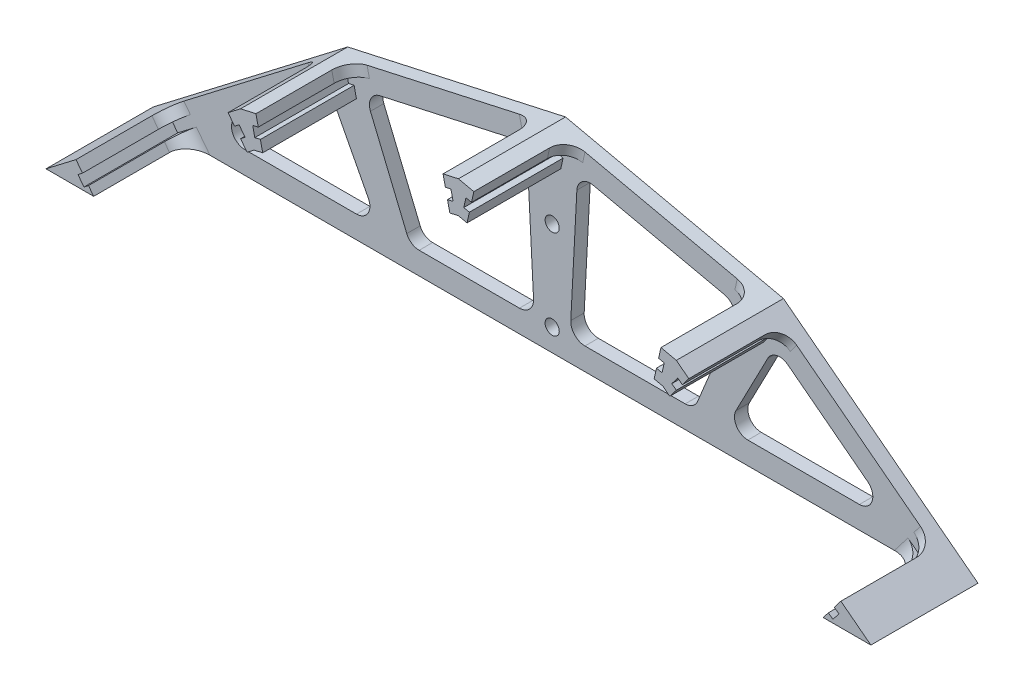
SolidWorks part; units mm, degrees
ref_plane "Front Plane" through (0, 0, 0) normal (0, 0, 1) x (1, 0, 0)
ref_plane "Top Plane" through (0, 0, 0) normal (0, 1, 0) x (1, 0, 0)
ref_plane "Right Plane" through (0, 0, 0) normal (1, 0, 0) x (0, 0, -1)
sketch "Sketch1" plane through (0, 0, 0) normal (0, 0, 1) x (1, 0, 0)
  line L0 (0, -57.7528) -> (0, 57.7528) construction
  line L2 (88.4825, 16.4928) -> (0, -57.7528) construction
  line L3 (0, 57.7528) -> (48.8148, 46.9308)
  line L4 (48.8148, 46.9308) -> (0, -57.7528) construction
  line L5 (48.8148, 46.9308) -> (88.4825, 16.4928)
  line L7 (-48.8148, 46.9308) -> (-88.4825, 16.4928)
  line L8 (-48.8148, 46.9308) -> (0, -57.7528) construction
  line L9 (0, 57.7528) -> (-48.8148, 46.9308)
  line L10 (-88.4825, 16.4928) -> (0, -57.7528) construction
  line L11 (-84.4891, 13.484) -> (84.4891, 13.484)
  line L12 (-84.4891, 13.484) -> (-92.4036, 13.484)
  line L13 (-92.4036, 13.484) -> (-88.4825, 16.4928)
  line L14 (84.4891, 13.484) -> (92.4036, 13.484)
  line L15 (92.4036, 13.484) -> (88.4825, 16.4928)
  dimension "D2" = 25
  dimension "D3" = 25
  dimension "D4" = 50
  dimension "D1" = 5
extrude "Boss-Extrude1" add sketch "Sketch1" along normal blind 3
sketch "Sketch2" plane through (0, 0, 3) normal (0, 0, 1) x (1, 0, 0)
  line L0 (-48.8148, 46.9308) -> (-45.3685, 47.6949)
  line L1 (0, 57.7528) -> (-48.8148, 46.9308) construction
  line L2 (-45.3685, 47.6949) -> (-44.849, 45.3518)
  line L3 (-43.8534, 40.8608) -> (-47.2997, 40.0968)
  line L4 (-47.2997, 40.0968) -> (-48.8148, 46.9308) construction
  line L5 (-3.8427, 53.316) -> (-1.4391, 53.8488) construction
  line L6 (1.5151, 50.9188) -> (0, 57.7528) construction
  line L7 (-1.9312, 50.1547) -> (1.5151, 50.9188)
  line L8 (-2.4507, 52.4978) -> (-1.9312, 50.1547)
  line L9 (-24.4074, 52.3418) -> (-20.3059, 33.8411) construction
  line L10 (0, 57.7528) -> (-48.8148, 46.9308) construction
  line L11 (-46.0987, 45.0747) -> (-45.6225, 42.9269)
  line L12 (-44.849, 45.3518) -> (-46.0987, 45.0747)
  line L13 (-43.4571, 44.5337) -> (-45.8606, 44.0008) construction
  line L14 (-44.3729, 43.2039) -> (-45.6225, 42.9269)
  line L15 (-44.3729, 43.2039) -> (-43.8534, 40.8608)
  line L16 (-2.4507, 52.4978) -> (-1.201, 52.7749)
  line L17 (-2.9269, 54.6457) -> (-1.6772, 54.9227)
  line L18 (-1.6772, 54.9227) -> (-1.201, 52.7749)
  line L19 (-3.4463, 56.9888) -> (-2.9269, 54.6457)
  line L20 (0, 57.7528) -> (-3.4463, 56.9888)
  line L21 (0, 57.7528) -> (0, -57.7528) construction
  line L22 (43.4571, 44.5337) -> (45.8606, 44.0008) construction
  line L23 (24.4074, 52.3418) -> (20.3059, 33.8411) construction
  line L24 (1.9312, 50.1547) -> (-1.5151, 50.9188)
  line L25 (-1.5151, 50.9188) -> (0, 57.7528) construction
  line L26 (3.8427, 53.316) -> (1.4391, 53.8488) construction
  line L27 (47.2997, 40.0968) -> (48.8148, 46.9308) construction
  line L28 (43.8534, 40.8608) -> (47.2997, 40.0968)
  line L29 (0, 57.7528) -> (3.4463, 56.9888)
  line L30 (3.4463, 56.9888) -> (2.9269, 54.6457)
  line L31 (1.6772, 54.9227) -> (1.201, 52.7749)
  line L32 (2.9269, 54.6457) -> (1.6772, 54.9227)
  line L33 (2.4507, 52.4978) -> (1.201, 52.7749)
  line L34 (44.3729, 43.2039) -> (43.8534, 40.8608)
  line L35 (44.3729, 43.2039) -> (45.6225, 42.9269)
  line L36 (44.849, 45.3518) -> (46.0987, 45.0747)
  line L37 (46.0987, 45.0747) -> (45.6225, 42.9269)
  line L38 (2.4507, 52.4978) -> (1.9312, 50.1547)
  line L39 (45.3685, 47.6949) -> (44.849, 45.3518)
  line L40 (48.8148, 46.9308) -> (45.3685, 47.6949)
  line L41 (48.8148, 46.9308) -> (0, -57.7528) construction
  line L42 (0, -57.7528) -> (-48.8148, 46.9308) construction
  line L43 (-82.2734, 13.2605) -> (-88.4825, 16.4928) construction
  line L44 (-50.4223, 41.2857) -> (-48.4692, 42.7844) construction
  line L45 (-68.6486, 31.7118) -> (-57.1127, 16.6778) construction
  line L46 (-81.4206, 13.0882) -> (-84.2211, 10.9393)
  line L47 (-84.2211, 10.9393) -> (-88.4825, 16.4928)
  line L48 (-82.6136, 16.5845) -> (-84.5668, 15.0858) construction
  line L49 (-44.5535, 41.3774) -> (-48.8148, 46.9308) construction
  line L50 (-47.354, 39.2284) -> (-44.5535, 41.3774)
  line L51 (-88.4825, 16.4928) -> (-85.6819, 18.6417)
  line L52 (-85.6819, 18.6417) -> (-84.2209, 16.7377)
  line L53 (-85.2364, 15.9584) -> (-83.8971, 14.2131)
  line L54 (-84.2209, 16.7377) -> (-85.2364, 15.9584)
  line L55 (-82.8816, 14.9923) -> (-83.8971, 14.2131)
  line L56 (-48.815, 41.1325) -> (-47.354, 39.2284)
  line L57 (-48.815, 41.1325) -> (-47.7995, 41.9117)
  line L58 (-50.1543, 42.8779) -> (-49.1388, 43.6571)
  line L59 (-49.1388, 43.6571) -> (-47.7995, 41.9117)
  line L60 (-82.8816, 14.9923) -> (-81.4206, 13.0882)
  line L61 (-51.6153, 44.7819) -> (-50.1543, 42.8779)
  line L62 (-48.8148, 46.9308) -> (-51.6153, 44.7819)
  line L63 (47.354, 39.2284) -> (44.5535, 41.3774)
  line L64 (44.5535, 41.3774) -> (48.8148, 46.9308) construction
  line L65 (82.6136, 16.5845) -> (84.5668, 15.0858) construction
  line L66 (84.2211, 10.9393) -> (88.4825, 16.4928)
  line L67 (81.4206, 13.0882) -> (84.2211, 10.9393)
  line L68 (68.6486, 31.7118) -> (57.1127, 16.6778) construction
  line L69 (50.4223, 41.2857) -> (48.4692, 42.7844) construction
  line L70 (48.8148, 46.9308) -> (51.6153, 44.7819)
  line L71 (51.6153, 44.7819) -> (50.1543, 42.8779)
  line L72 (82.8816, 14.9923) -> (81.4206, 13.0882)
  line L73 (49.1388, 43.6571) -> (47.7995, 41.9117)
  line L74 (50.1543, 42.8779) -> (49.1388, 43.6571)
  line L75 (48.815, 41.1325) -> (47.7995, 41.9117)
  line L76 (48.815, 41.1325) -> (47.354, 39.2284)
  line L77 (82.8816, 14.9923) -> (83.8971, 14.2131)
  line L78 (84.2209, 16.7377) -> (85.2364, 15.9584)
  line L79 (85.2364, 15.9584) -> (83.8971, 14.2131)
  line L80 (85.6819, 18.6417) -> (84.2209, 16.7377)
  line L81 (88.4825, 16.4928) -> (85.6819, 18.6417)
  line L82 (-43.4571, 44.5337) -> (-50.1313, 43.054) construction
  line L83 (-88.4825, 16.4928) -> (-92.4036, 13.484)
  line L84 (-92.4036, 13.484) -> (-86.1738, 13.484)
  line L85 (-92.4036, 13.484) -> (92.4036, 13.484) construction
  line L86 (-86.1738, 13.484) -> (-88.4825, 16.4928)
  line L87 (84.2211, 10.9393) -> (88.4825, 16.4928)
  line L88 (92.4036, 13.484) -> (86.1738, 13.484)
  line L89 (88.4825, 16.4928) -> (92.4036, 13.484)
  point P20 (-40.7831, 32.3513)
  point P94 (-48.0573, 43.5138)
  dimension "D1" = 7
  dimension "D2" = 22.75
  dimension "D3" = 1.1
  dimension "D4" = 1.28
extrude "Boss-Extrude2" add sketch "Sketch2" along normal blind 21
sketch "Sketch3" plane through (0, 0, 3) normal (0, 0, 1) x (1, 0, 0)
  line L0 (0, -57.7528) -> (-77.6741, 18.484) construction
  line L1 (-70.6626, 23.8641) -> (-52.7995, 37.5709)
  line L2 (-48.3122, 36.5761) -> (-41.1769, 22.8693)
  line L3 (-43.8379, 18.484) -> (-68.8363, 18.484)
  line L4 (-32.5703, 20.336) -> (-40.7148, 39.9987)
  line L5 (-38.5925, 44.0757) -> (-9.1783, 50.5967)
  line L6 (-5.5331, 47.8248) -> (-4.1705, 21.8252)
  line L7 (-7.3412, 18.484) -> (-29.7986, 18.484)
  line L8 (-48.8148, 46.9308) -> (-88.4825, 16.4928) construction
  line L9 (0, 57.7528) -> (-48.8148, 46.9308) construction
  line L10 (-84.4891, 13.484) -> (84.4891, 13.484) construction
  line L11 (-48.8148, 46.9308) -> (0, -57.7528) construction
  line L12 (0, -57.7528) -> (0, 57.7528) construction
  line L13 (-4.1705, 21.8252) -> (0, -57.7528) construction
  line L14 (0, 57.7528) -> (0, 0) construction
  line L15 (7.3412, 18.484) -> (29.7986, 18.484)
  line L16 (5.5331, 47.8248) -> (4.1705, 21.8252)
  line L17 (38.5925, 44.0757) -> (9.1783, 50.5967)
  line L18 (32.5703, 20.336) -> (40.7148, 39.9987)
  line L19 (43.8379, 18.484) -> (68.8363, 18.484)
  line L20 (48.3122, 36.5761) -> (41.1769, 22.8693)
  line L21 (70.6626, 23.8641) -> (52.7995, 37.5709)
  line L22 (-81.7243, 13.484) -> (81.7243, 13.484) construction
  line L23 (-48.8148, 46.9308) -> (0, -57.7528) construction
  line L24 (0, -57.7528) -> (48.8148, 46.9308) construction
  arc A0 (-43.8379, 18.484) -> (-41.1769, 22.8693) centre (-43.8379, 21.484) ccw
  arc A1 (-52.7995, 37.5709) -> (-48.3122, 36.5761) centre (-50.9733, 35.1908) cw
  arc A2 (-70.6626, 23.8641) -> (-68.8363, 18.484) centre (-68.8363, 21.484) ccw
  arc A3 (-32.5703, 20.336) -> (-29.7986, 18.484) centre (-29.7986, 21.484) ccw
  arc A4 (-40.7148, 39.9987) -> (-38.5925, 44.0757) centre (-37.9432, 41.1468) cw
  arc A5 (-9.1783, 50.5967) -> (-5.5331, 47.8248) centre (-8.529, 47.6678) cw
  arc A6 (-4.1705, 21.8252) -> (-7.3412, 18.484) centre (-7.3412, 21.659) cw
  arc A7 (4.1705, 21.8252) -> (7.3412, 18.484) centre (7.3412, 21.659) ccw
  arc A8 (9.1783, 50.5967) -> (5.5331, 47.8248) centre (8.529, 47.6678) ccw
  arc A9 (40.7148, 39.9987) -> (38.5925, 44.0757) centre (37.9432, 41.1468) ccw
  arc A10 (32.5703, 20.336) -> (29.7986, 18.484) centre (29.7986, 21.484) cw
  arc A11 (70.6626, 23.8641) -> (68.8363, 18.484) centre (68.8363, 21.484) cw
  arc A12 (52.7995, 37.5709) -> (48.3122, 36.5761) centre (50.9733, 35.1908) ccw
  arc A13 (43.8379, 18.484) -> (41.1769, 22.8693) centre (43.8379, 21.484) cw
  circle A14 centre (0, 18.484) radius 1.5875
  circle A15 centre (0, 38.484) radius 1.5875
  point P64 (48.8148, 46.9308)
  point P66 (-48.8148, 46.9308)
  dimension "D1" = 5
  dimension "D6" = 3
  dimension "D7" = 3
  dimension "D8" = 3.175
  dimension "D12" = 3.175
  dimension "D2" = 5
  dimension "D3" = 5
  dimension "D4" = 2.5
  dimension "D5" = 2.5
  dimension "D9" = 3
  dimension "D10" = 20
  dimension "D11" = 5
extrude "Cut-Extrude1" cut sketch "Sketch3" against normal through all
fillet "Fillet3" radius 4 1 edges at (-84.9514, 17.6897, 3)
fillet "Fillet4" radius 4 9 edges at (84.9514, 17.6897, 3) (50.8848, 43.8299, 3) (45.1087, 46.5233, 3) (3.1866, 55.8172, 3) (-3.1866, 55.8172, 3) (-82.303, 14.2381, 3) (82.303, 14.2381, 3)
equation "\"D3@Sketch1\"=\"D2@Sketch1\""
equation "\"D5@Sketch3\"=\"D4@Sketch3\""
